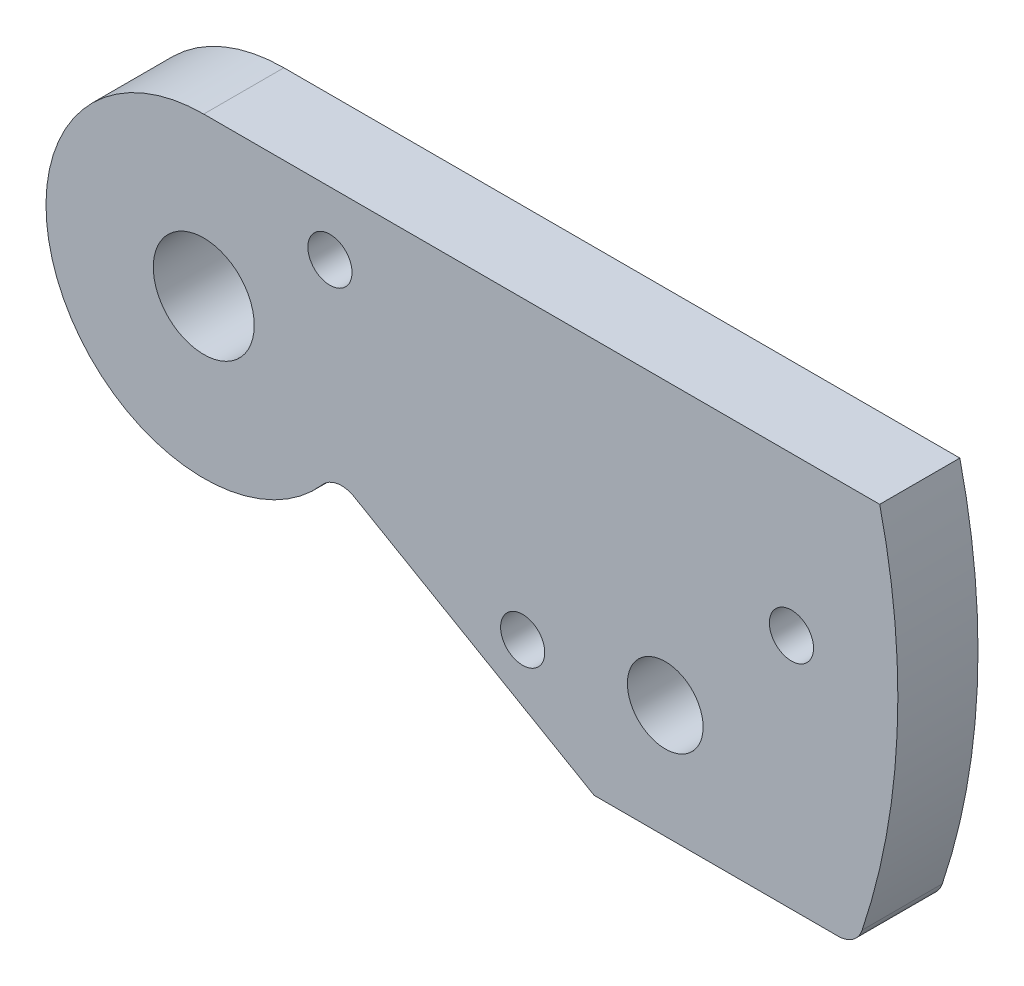
SolidWorks part; units mm, degrees
material "6061-T6 (SS)"
ref_plane "Front Plane" through (0, 0, 0) normal (0, 0, 1) x (1, 0, 0)
ref_plane "Top Plane" through (0, 0, 0) normal (0, 1, 0) x (1, 0, 0)
ref_plane "Right Plane" through (0, 0, 0) normal (1, 0, 0) x (0, 0, -1)
sketch "Sketch1" plane through (0, 0, 0) normal (0, 0, 1) x (1, 0, 0)
  line L0 (0, 0) -> (340.6, 0) construction
  line L1 (340.6, 0) -> (373.509, 19) construction
  line L2 (340.6, 0) -> (307.691, 19) construction
  line L3 (340.6, 0) -> (377.1687, -9.7841) construction
  line L5 (-50, -75) -> (450, -75)
  line L6 (-50, -75) -> (-50, 75)
  line L7 (-50, 75) -> (450, 75)
  line L8 (450, -75) -> (450, 75)
  circle A0 centre (0, 0) radius 9.3
  circle A1 centre (340.6, 0) radius 4
  circle A2 centre (373.509, 19) radius 4.5
  circle A3 centre (307.691, 19) radius 4.5
  circle A4 centre (377.1687, -9.7841) radius 3
  circle A5 centre (340.6, 0) radius 42.5
  circle A6 centre (340.6, 0) radius 33.5
  dimension "D1" = 340.6
  dimension "D2" = 36.5687
  dimension "D6" = 8
  dimension "D7" = 6
  dimension "D8" = 9
  dimension "D9" = 9
  dimension "D12" = 18.6
  dimension "D3" = 9.7841
  dimension "D4" = 150
  dimension "D5" = 120
  dimension "D10" = 38
  dimension "D11" = 38
  dimension "D13" = 150
  dimension "D14" = 500
  dimension "D15" = 75
  dimension "D16" = 50
extrude "Boss-Extrude1" add sketch "Sketch1" along normal blind 6.35 contours L5 L8 L7 L6 A5 A0 | A6 A3 A5 A2 A4 | A6 A1
sketch "Sketch3" plane through (0, 0, 6.35) normal (0, 0, 1) x (1, 0, 0)
  line L0 (-50, 55) -> (450, 55)
  line L1 (340.6, 0) -> (351.0029, -6.9303) construction
  line L2 (-50, -75) -> (-50, 75) construction
  line L3 (450, -75) -> (450, 75) construction
  line L4 (-9.0863, 9.0863) -> (36.8274, 55)
  line L5 (0, 0) -> (-9.0863, 9.0863) construction
  line L6 (0, 0) -> (9.0863, -9.0863) construction
  line L7 (-50, 3) -> (450, 3) construction
  line L8 (9.0863, -9.0863) -> (21.1726, 3)
  line L9 (30.8962, 3) -> (328.4653, 3)
  line L10 (450, -18.7841) -> (-50, -18.7841) construction
  line L11 (351.0029, -6.9303) -> (371.5323, -18.7841)
  line L12 (371.5323, -18.7841) -> (392.2929, -18.7841)
  line L13 (21.1726, 3) -> (30.8962, 3)
  circle A0 centre (0, 0) radius 12.85
  circle A1 centre (377.1687, -9.7841) radius 3 construction
  circle A2 centre (340.6, 0) radius 12.5
  circle A3 centre (340.6, 0) radius 55
  dimension "D1" = 25.7
  dimension "D4" = 9
  dimension "D5" = 25
  dimension "D2" = 55
  dimension "D3" = 3
  dimension "D6" = 23.7059
  dimension "D7" = 149.998
  dimension "D8" = 45
  dimension "D10" = 180
extrude "Cut-Extrude1" cut sketch "Sketch3" against normal blind 7
sketch "Sketch4" plane through (0, 0, 6.35) normal (0, 0, 1) x (1, 0, 0)
  line L0 (0, 0) -> (55, 55) construction
  line L1 (36.8274, 55) -> (340.6, 55) construction
  line L3 (6.47, 24.6427) -> (23.1127, 8)
  line L4 (-9.0863, 9.0863) -> (36.8274, 55) construction
  line L5 (15.7908, 8) -> (84.2458, 8) construction
  line L6 (21.1726, 3) -> (328.4653, 3) construction
  line L7 (41, 3) -> (41, 8)
  line L8 (23.1127, 8) -> (41, 8)
  line L9 (50.8274, 55) -> (50.8274, 49)
  line L10 (50.8274, 49) -> (30.8274, 49)
  line L11 (50.8274, 55) -> (36.8274, 55)
  line L12 (36.8274, 55) -> (30.8274, 49)
  line L13 (41, 3) -> (21.1726, 3)
  line L14 (21.1726, 3) -> (9.0863, -9.0863)
  line L15 (6.47, 24.6427) -> (-9.0863, 9.0863)
  circle A1 centre (0, 0) radius 12.85
  line M7 (36.8274, 55) -> (-9.0863, 9.0863)
  arc M8 (-9.0863, 9.0863) -> (9.0863, -9.0863) centre (0, 0) ccw
  line M9 (9.0863, -9.0863) -> (21.1726, 3)
  line M10 (21.1726, 3) -> (328.4653, 3)
  line M15 (340.6, 55) -> (36.8274, 55)
  circle M20 centre (0, 0) radius 9.3
  dimension "D1" = 22
  dimension "D2" = 5
  dimension "D3" = 41
  dimension "D4" = 23.5363
  dimension "D5" = 6
  dimension "D6" = 20
extrude "Cut-Extrude2" cut sketch "Sketch4" against normal blind 10 contours A1 L7 L8 L3 M9 M10 M7 | A1 M8 M20 | L10 L9 M15 M7
fillet "Fillet1" radius 2 3 edges at (392.2929, -18.7841, 3.175) (328.4653, 3, 3.175) (351.0029, -6.9303, 3.175)
sketch "Sketch5" plane through (0, 0, 6.35) normal (0, 0, 1) x (1, 0, 0)
  line L0 (340.6, 12.5) -> (394.1607, 12.5)
  circle A0 centre (340.6, 0) radius 12.5
  circle A1 centre (340.6, 0) radius 55
  arc M3 (303.7939, 21.25) -> (377.4061, 21.25) centre (340.6, 0) cw
  arc M4 (377.4061, 21.25) -> (369.6119, 16.75) centre (373.509, 19) cw
  arc M5 (369.6119, 16.75) -> (311.5881, 16.75) centre (340.6, 0) ccw
  arc M6 (311.5881, 16.75) -> (303.7939, 21.25) centre (307.691, 19) cw
  arc M9 (392.7693, -17.4175) -> (340.6, 55) centre (340.6, 0) ccw
  line M10 (340.6, 55) -> (50.8274, 55)
  line M11 (50.8274, 55) -> (50.8274, 49)
  line M12 (50.8274, 49) -> (30.8274, 49)
  line M13 (30.8274, 49) -> (6.47, 24.6427)
  line M14 (6.47, 24.6427) -> (23.1127, 8)
  line M15 (23.1127, 8) -> (41, 8)
  line M16 (41, 8) -> (41, 3)
  line M17 (41, 3) -> (326.1345, 3)
  arc M18 (326.1345, 3) -> (328.1298, 0.8621) centre (326.1345, 1) cw
  dimension "D1" = 25
  dimension "D2" = 110
extrude "Cut-Extrude4" cut sketch "Sketch5" against normal blind 10 contours A1 M10 M11 M12 M13 M14 M15 M16 M17 | A1 A0 L0 M9 M17 M18 M6 M3 M4 M5
sketch "Sketch6" plane through (0, 0, 6.35) normal (0, 0, 1) x (1, 0, 0)
  line L0 (340.6, 0) -> (395.6, 0) construction
  line L1 (350.6, 7.5) -> (387.1687, 0) construction
  line L2 (387.1687, 0) -> (368.8843, 3.75) construction
  line L3 (368.8843, 3.75) -> (365.0325, -15.0311) construction
  line L4 (352.5208, -7.8068) -> (371.5323, -18.7841) construction
  circle A0 centre (350.6, 7.5) radius 1.75
  arc A1 (392.7693, -17.4175) -> (394.1607, 12.5) centre (340.6, 0) ccw construction
  circle A2 centre (387.1687, 0) radius 1.75
  circle A3 centre (377.1687, -9.7841) radius 3
  circle A4 centre (365.8707, -10.9441) radius 1.75
  dimension "D1" = 3.5
  dimension "D2" = 3.5
  dimension "D6" = 3.5
  dimension "D3" = 10
  dimension "D4" = 7.5
  dimension "D5" = 10
  dimension "D7" = 15
extrude "Cut-Extrude5" cut sketch "Sketch6" against normal blind 10
